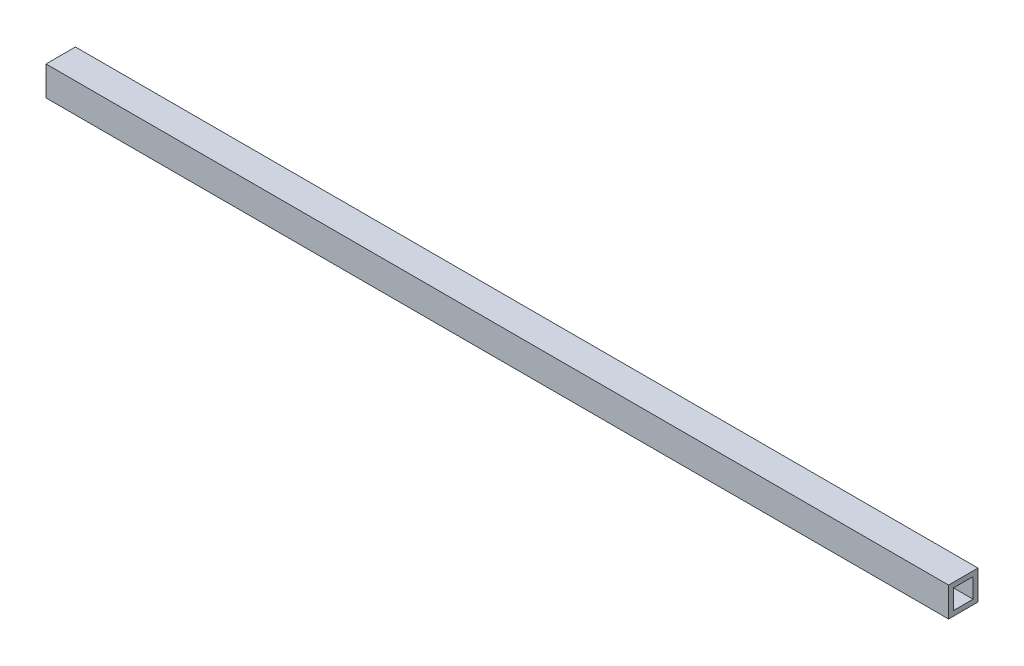
SolidWorks part; units mm, degrees
ref_plane "Front Plane" through (0, 0, 0) normal (0, 0, 1) x (1, 0, 0)
ref_plane "Top Plane" through (0, 0, 0) normal (0, 1, 0) x (1, 0, 0)
ref_plane "Right Plane" through (0, 0, 0) normal (1, 0, 0) x (0, 0, -1)
sketch "Sketch1" plane through (0, 0, 0) normal (1, 0, 0) x (0, 0, -1)
  line L1 (0, 0) -> (12.7, 0)
  line L2 (0, 0) -> (0, 12.7)
  line L3 (0, 12.7) -> (12.7, 12.7)
  line L4 (12.7, 0) -> (12.7, 12.7)
  dimension "D1" = 12.7
  dimension "D2" = 12.7
extrude "Extrude-Thin1" add sketch "Sketch1" along normal blind 584.2 thin
